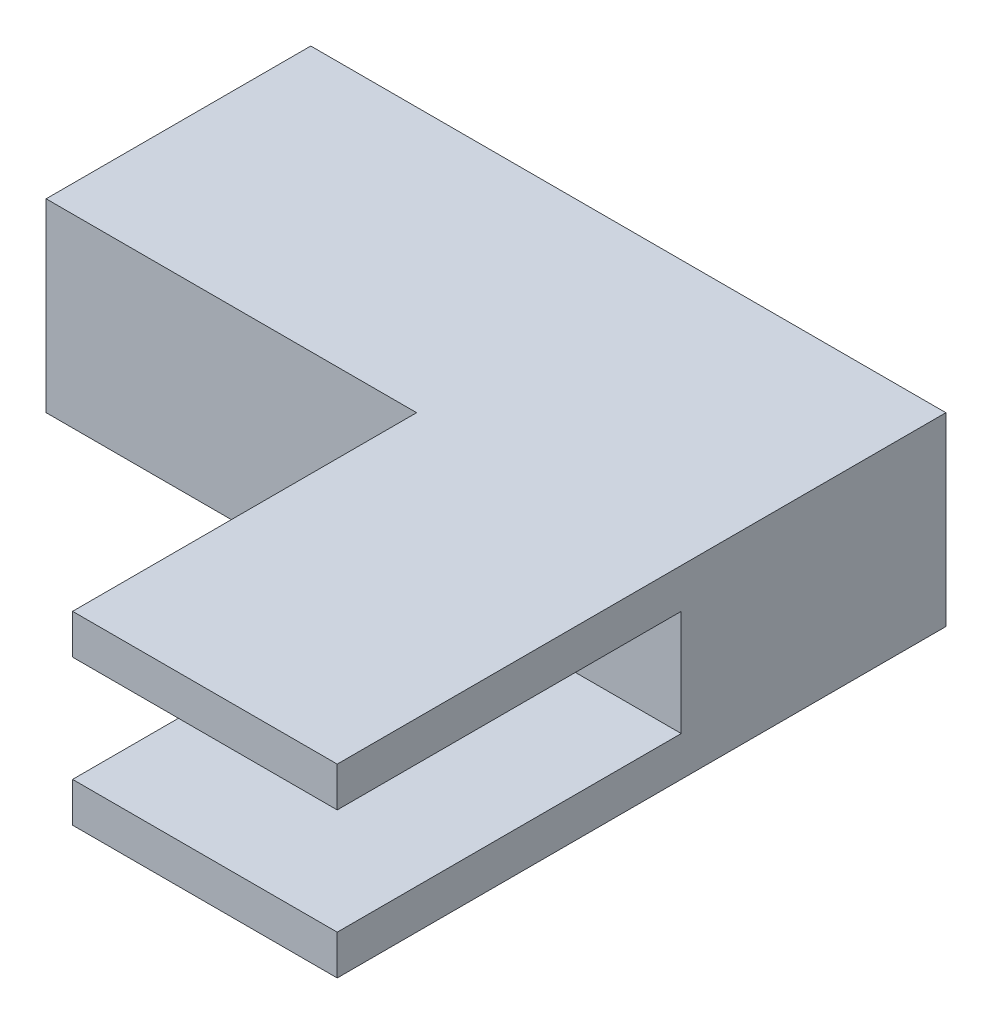
SolidWorks part; units mm, degrees
ref_plane "Front Plane" through (0, 0, 0) normal (0, 0, 1) x (1, 0, 0)
ref_plane "Top Plane" through (0, 0, 0) normal (0, 1, 0) x (1, 0, 0)
ref_plane "Right Plane" through (0, 0, 0) normal (1, 0, 0) x (0, 0, -1)
sketch "Sketch3" plane through (0, 0, 0) normal (0, 1, 0) x (1, 0, 0)
  line L1 (-12, 11.5) -> (12, 11.5)
  line L2 (-12, 11.5) -> (-12, -11.5)
  line L3 (-12, -11.5) -> (12, -11.5)
  line L4 (12, 11.5) -> (12, -11.5)
  line L5 (-12, 11.5) -> (12, -11.5) construction
  line L6 (-12, -11.5) -> (12, 11.5) construction
  line L7 (-12, -11.5) -> (2, -11.5)
  line L8 (-12, -11.5) -> (-12, 1.5)
  line L9 (-12, 1.5) -> (2, 1.5)
  line L10 (2, -11.5) -> (2, 1.5)
  point P0 (0, 0)
  dimension "D1" = 14
  dimension "D2" = 13
  dimension "D3" = 10
  dimension "D4" = 10
extrude "Boss-Extrude2" add sketch "Sketch3" against normal blind 7 contours L10 L3 L4 L1 L2 L9
sketch "Sketch4" plane through (0, 0, 11.5) normal (0, 0, 1) x (1, 0, 0)
  line L0 (12, -7) -> (12, 0) construction
  line L1 (12, -1.5) -> (-12, -1.5)
  line L2 (12, -1.5) -> (12, -5.5)
  line L3 (12, -5.5) -> (-12, -5.5)
  line L4 (-12, -1.5) -> (-12, -5.5)
  line L5 (-12, -7) -> (-12, 0) construction
  line L6 (-12, 0) -> (2, 0) construction
  dimension "D1" = 1.5
  dimension "D2" = 4
extrude "Cut-Extrude1" cut sketch "Sketch4" against normal up to surface (13 mm away) up to face at (-5, -3.5, -1.5)
